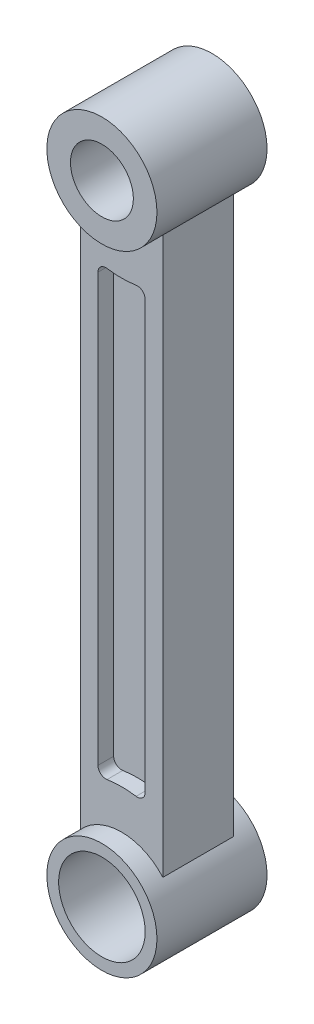
SolidWorks part; units mm, degrees
ref_plane "Front Plane" through (0, 0, 0) normal (0, 0, 1) x (1, 0, 0)
ref_plane "Top Plane" through (0, 0, 0) normal (0, 1, 0) x (1, 0, 0)
ref_plane "Right Plane" through (0, 0, 0) normal (1, 0, 0) x (0, 0, -1)
sketch "Sketch1" plane through (0, 0, 0) normal (0, 0, 1) x (1, 0, 0)
  circle A0 centre (0, 0) radius 7
  circle A1 centre (0, 0) radius 5.5
  dimension "D1" = 11
  dimension "A" = 14
extrude "Boss-Extrude1" add sketch "Sketch1" along normal mid plane 14
sketch "Sketch2" plane through (0, 0, 0) normal (0, 0, 1) x (1, 0, 0)
  circle A0 centre (0, 80) radius 7
  circle A1 centre (0, 80) radius 4
  dimension "D1" = 14
  dimension "D2" = 8
  dimension "D3" = 80
extrude "Boss-Extrude2" add sketch "Sketch2" along normal mid plane 14 separate body
sketch "Sketch3" plane through (0, 0, 0) normal (0, 0, 1) x (1, 0, 0)
  line L0 (-5.25, 75.3699) -> (-5.25, 4.6301)
  line L1 (5.25, 75.3699) -> (5.25, 4.6301)
  line L2 (0, -7.7) -> (0, 7.7) construction
  circle A0 centre (0, 80) radius 7 construction
  circle A1 centre (0, 0) radius 7 construction
  arc A2 (-5.25, 75.3699) -> (5.25, 75.3699) centre (0, 80) ccw
  arc A3 (-5.25, 4.6301) -> (5.25, 4.6301) centre (0, 0) cw
  dimension "D1" = 5.25
  dimension "D2" = 5.25
extrude "Boss-Extrude3" add sketch "Sketch3" along normal mid plane 9
sketch "Sketch4" plane through (0, 0, 4.5) normal (0, 0, 1) x (1, 0, 0)
  line L0 (-3, 67.1548) -> (-3, 12.8452)
  line L1 (3, 67.1548) -> (3, 12.8452)
  line L2 (-5.25, 75.3699) -> (-5.25, 4.6301) construction
  line L3 (5.25, 4.6301) -> (5.25, 75.3699) construction
  arc A0 (-1.8462, 68.1429) -> (1.8462, 68.1429) centre (0, 80) ccw
  arc A1 (-1.8462, 11.8571) -> (1.8462, 11.8571) centre (0, 0) cw
  circle A2 centre (0, 0) radius 7 construction
  circle A3 centre (0, 80) radius 7 construction
  circle A4 centre (0, 0) radius 7
  circle A5 centre (0, 80) radius 7
  arc A6 (3, 12.8452) -> (1.8462, 11.8571) centre (2, 12.8452) cw
  arc A7 (-3, 12.8452) -> (-1.8462, 11.8571) centre (-2, 12.8452) ccw
  arc A8 (3, 67.1548) -> (1.8462, 68.1429) centre (2, 67.1548) ccw
  arc A9 (-3, 67.1548) -> (-1.8462, 68.1429) centre (-2, 67.1548) cw
  dimension "D1" = 5
  dimension "D2" = 5
  dimension "D5" = 1
  dimension "D3" = 2.25
  dimension "D4" = 2.25
extrude "Cut-Extrude2" cut sketch "Sketch4" against normal blind 2 contours A9 L0 A7 A1 A6 L1 A8 A0
mirror "Mirror1" about plane through (0, 0, 0) normal (0, 0, 1) of "Cut-Extrude2"
equation "\"A\"=14"
equation "\"B\"= \"A\" / 2 + 2"
equation "\"C\"= \"B\" - 4"
equation "\"D1@Sketch2\"=\"A\""
equation "\"D1@Boss-Extrude3\"=\"B\""
